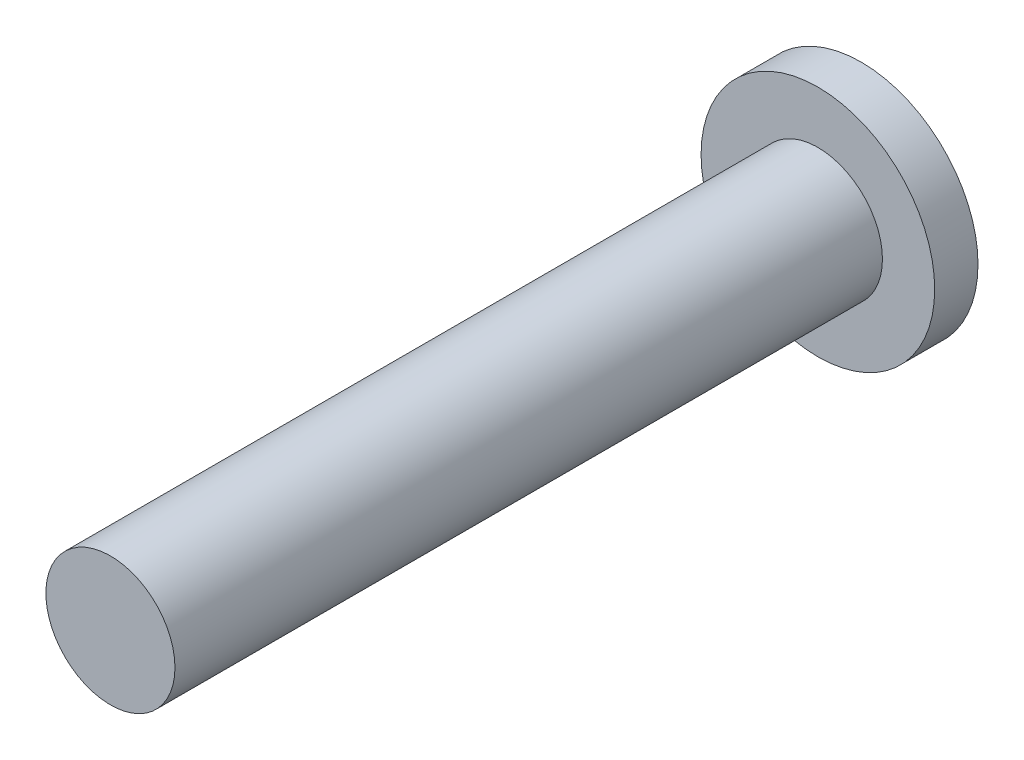
SolidWorks part; units mm, degrees
ref_plane "Front Plane" through (0, 0, 0) normal (0, 0, 1) x (1, 0, 0)
ref_plane "Top Plane" through (0, 0, 0) normal (0, 1, 0) x (1, 0, 0)
ref_plane "Right Plane" through (0, 0, 0) normal (1, 0, 0) x (0, 0, -1)
sketch "Sketch1" plane through (0, 0, 0) normal (0, 0, 1) x (1, 0, 0)
  circle A0 centre (0, 0) radius 4.425
  dimension "D1" = 8.85
extrude "Boss-Extrude1" add sketch "Sketch1" along normal blind 1.64
sketch "Sketch2" plane through (0, 0, 1.64) normal (0, 0, 1) x (1, 0, 0)
  circle A0 centre (0, 0) radius 2.445
  dimension "D1" = 4.89
extrude "Boss-Extrude2" add sketch "Sketch2" along normal blind 26.8
